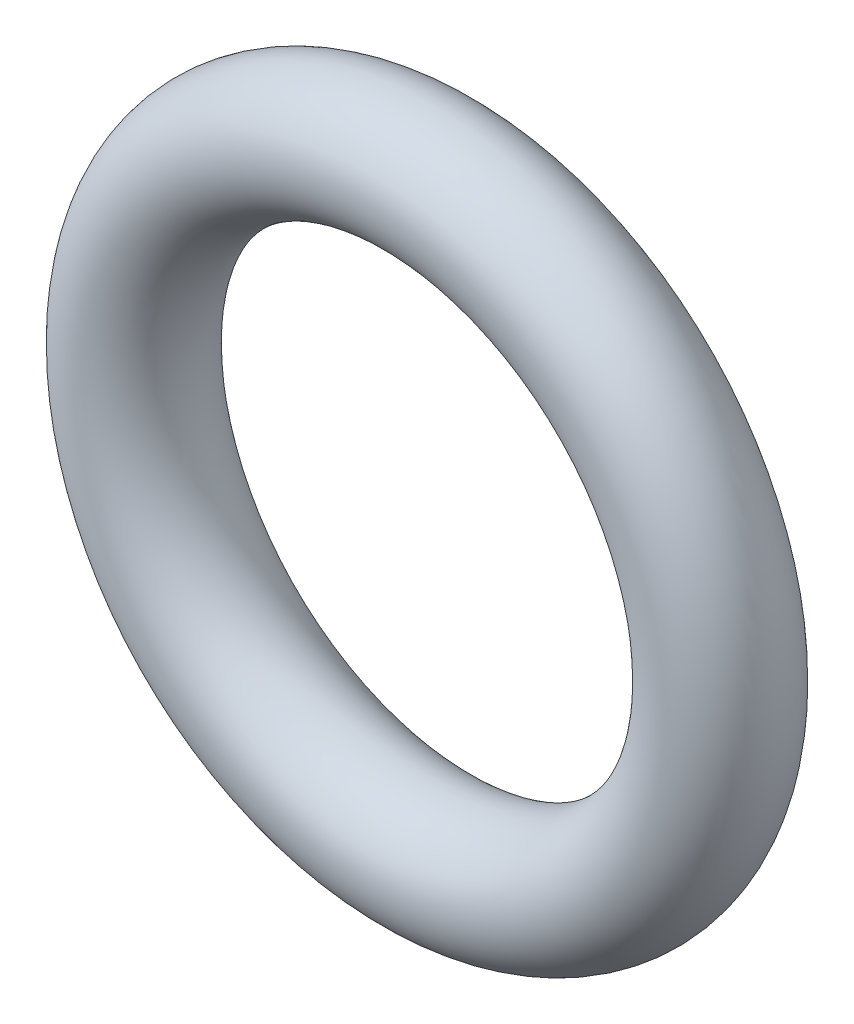
SolidWorks part; units mm, degrees
ref_plane "Front" through (0, 0, 0) normal (0, 0, 1) x (1, 0, 0)
ref_plane "Top" through (0, 0, 0) normal (0, 1, 0) x (1, 0, 0)
ref_plane "Right" through (0, 0, 0) normal (1, 0, 0) x (0, 0, -1)
sketch "Sketch1" plane through (0, 0, 0) normal (1, 0, 0) x (0, -1, 0)
  line L0 (0, -0.8128) -> (0, 0.8128) construction
  line L2 (-5.127, 0) -> (5.127, 0) construction
  line L3 (-3.0353, 0) -> (3.0353, 0) construction
  circle A0 centre (3.8481, 0) radius 0.8128
  point P2 (0, 0)
  point P9 (3.0353, 0)
  point P10 (4.6609, 0)
  point P13 (3.8481, 0.8128)
  point P14 (3.8481, -0.8128)
  dimension "Width" = 1.6256
  dimension "ID" = 6.0706
revolve "Revolve1" add sketch "Sketch1" angle 360 about L0
sketch "Sketch2" plane through (0, 0, 0) normal (0, 0, 1) x (1, 0, 0)
  circle A0 centre (0, 0) radius 3.0353
